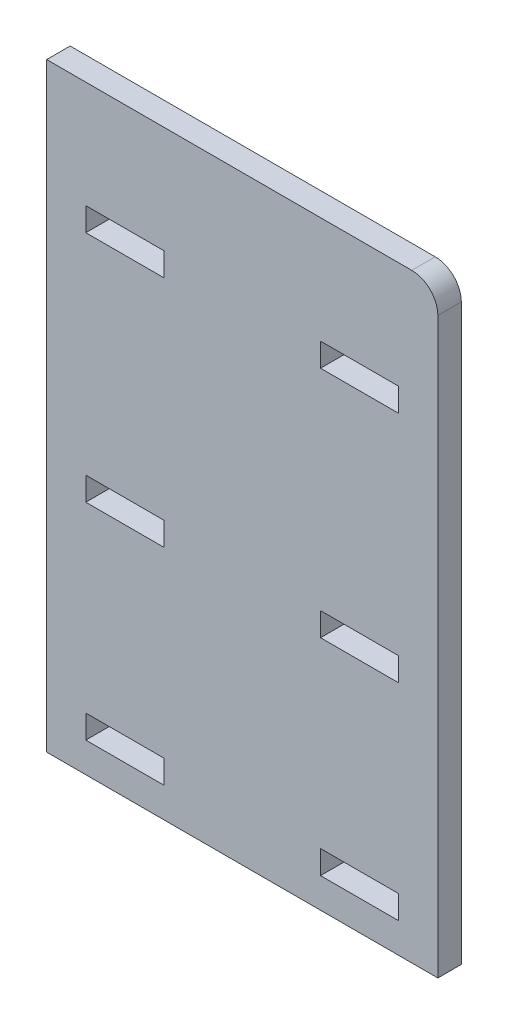
SolidWorks part; units mm, degrees
ref_plane "Front Plane" through (0, 0, 0) normal (0, 0, 1) x (1, 0, 0)
ref_plane "Top Plane" through (0, 0, 0) normal (0, 1, 0) x (1, 0, 0)
ref_plane "Right Plane" through (0, 0, 0) normal (1, 0, 0) x (0, 0, -1)
sketch "Sketch1" plane through (0, 0, 0) normal (0, 0, 1) x (1, 0, 0)
  line L0 (0, 57.5) -> (0, 35)
  line L1 (-37.5, 57.5) -> (37.5, 57.5)
  line L2 (-37.5, 57.5) -> (-37.5, -57.5)
  line L3 (-37.5, -57.5) -> (37.5, -57.5)
  line L4 (37.5, 57.5) -> (37.5, -57.5)
  line L5 (-37.5, 57.5) -> (37.5, -57.5) construction
  line L6 (-37.5, -57.5) -> (37.5, 57.5) construction
  line L8 (15, 37) -> (15, 32.5)
  line L9 (-30, 37) -> (-15, 37)
  line L10 (-30, 37) -> (-30, 32.5)
  line L11 (-30, 32.5) -> (-15, 32.5)
  line L12 (-15, 37) -> (-15, 32.5)
  line L13 (-30, 37) -> (-15, 32.5) construction
  line L14 (-30, 32.5) -> (-15, 37) construction
  line L15 (30, 32.5) -> (15, 32.5)
  line L16 (30, 37) -> (30, 32.5)
  line L17 (30, 37) -> (15, 37)
  line L18 (0, 57.5) -> (0, -10)
  line L19 (-37.5, -10) -> (-22.5, -10)
  line L20 (15, -7.75) -> (15, -12.25)
  line L21 (-30, -7.75) -> (-15, -7.75)
  line L22 (-30, -7.75) -> (-30, -12.25)
  line L23 (-30, -12.25) -> (-15, -12.25)
  line L24 (-15, -7.75) -> (-15, -12.25)
  line L25 (-30, -7.75) -> (-15, -12.25) construction
  line L26 (-30, -12.25) -> (-15, -7.75) construction
  line L27 (30, -12.25) -> (15, -12.25)
  line L28 (30, -7.75) -> (30, -12.25)
  line L29 (30, -7.75) -> (15, -7.75)
  line L30 (0, 57.5) -> (0, -49.5)
  line L31 (-37.5, -49.5) -> (-22.5, -49.5)
  line L32 (30, -51.75) -> (15, -51.75)
  line L33 (-30, -47.25) -> (-15, -47.25)
  line L34 (-30, -47.25) -> (-30, -51.75)
  line L35 (-30, -51.75) -> (-15, -51.75)
  line L36 (-15, -47.25) -> (-15, -51.75)
  line L37 (-30, -47.25) -> (-15, -51.75) construction
  line L38 (-30, -51.75) -> (-15, -47.25) construction
  line L39 (15, -47.25) -> (15, -51.75)
  line L40 (30, -47.25) -> (15, -47.25)
  line L41 (30, -47.25) -> (30, -51.75)
  point P0 (0, 0)
  point P8 (-22.5, 34.75)
  dimension "D1" = 75
  dimension "D2" = 115
  dimension "D3" = 22.5
  dimension "D4" = 22.75
  dimension "D5" = 4.5
  dimension "D6" = 15
  dimension "D7" = 67.5
  dimension "D8" = 15
  dimension "D9" = 4.5
  dimension "D10" = 15
  dimension "D11" = 107
  dimension "D12" = 15
  dimension "D13" = 4.5
extrude "Boss-Extrude1" add sketch "Sketch1" along normal blind 4.5
fillet "Fillet1" radius 5 1 edges at (37.5, 57.5, 2.25)
